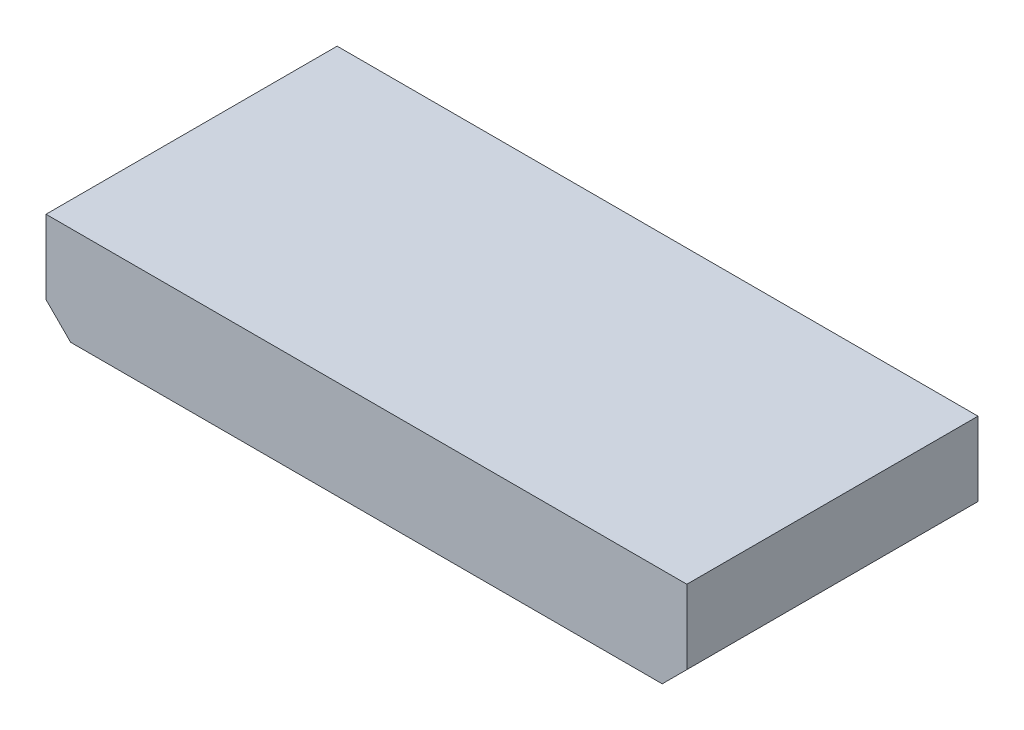
SolidWorks part; units mm, degrees
ref_plane "Front Plane" through (0, 0, 0) normal (0, 0, 1) x (1, 0, 0)
ref_plane "Top Plane" through (0, 0, 0) normal (0, 1, 0) x (1, 0, 0)
ref_plane "Right Plane" through (0, 0, 0) normal (1, 0, 0) x (0, 0, -1)
sketch "Sketch1" plane through (0, 0, 0) normal (0, 0, 1) x (1, 0, 0)
  line L0 (-5.08, 2.54) -> (-5.08, -1.27)
  line L1 (-5.08, -1.27) -> (-3.81, -2.54)
  line L2 (-3.81, -2.54) -> (26.67, -2.54)
  line L3 (26.67, -2.54) -> (27.94, -1.27)
  line L4 (27.94, -1.27) -> (27.94, 2.54)
  line L5 (27.94, 2.54) -> (-5.08, 2.54)
extrude "Component_Outline" add sketch "Sketch1" along normal blind 15 separate body
sketch "Sketch2" plane through (0, 0, 0) normal (0, 0, 1) x (1, 0, 0)
  circle A0 centre (0, 0) radius 0.25
extrude "1" add sketch "Sketch2" against normal blind 2 separate body
sketch "Sketch3" plane through (0, 0, 0) normal (0, 0, 1) x (1, 0, 0)
  circle A0 centre (2.54, 0) radius 0.25
extrude "2" add sketch "Sketch3" against normal blind 2 separate body
sketch "Sketch4" plane through (0, 0, 0) normal (0, 0, 1) x (1, 0, 0)
  circle A0 centre (5.08, 0) radius 0.25
extrude "3" add sketch "Sketch4" against normal blind 2 separate body
sketch "Sketch5" plane through (0, 0, 0) normal (0, 0, 1) x (1, 0, 0)
  circle A0 centre (7.62, 0) radius 0.25
extrude "4" add sketch "Sketch5" against normal blind 2 separate body
sketch "Sketch6" plane through (0, 0, 0) normal (0, 0, 1) x (1, 0, 0)
  circle A0 centre (10.16, 0) radius 0.25
extrude "5" add sketch "Sketch6" against normal blind 2 separate body
sketch "Sketch7" plane through (0, 0, 0) normal (0, 0, 1) x (1, 0, 0)
  circle A0 centre (12.7, 0) radius 0.25
extrude "6" add sketch "Sketch7" against normal blind 2 separate body
sketch "Sketch8" plane through (0, 0, 0) normal (0, 0, 1) x (1, 0, 0)
  circle A0 centre (15.24, 0) radius 0.25
extrude "7" add sketch "Sketch8" against normal blind 2 separate body
sketch "Sketch9" plane through (0, 0, 0) normal (0, 0, 1) x (1, 0, 0)
  circle A0 centre (17.78, 0) radius 0.25
extrude "8" add sketch "Sketch9" against normal blind 2 separate body
sketch "Sketch10" plane through (0, 0, 0) normal (0, 0, 1) x (1, 0, 0)
  circle A0 centre (20.32, 0) radius 0.25
extrude "9" add sketch "Sketch10" against normal blind 2 separate body
sketch "Sketch11" plane through (0, 0, 0) normal (0, 0, 1) x (1, 0, 0)
  circle A0 centre (22.86, 0) radius 0.25
extrude "10" add sketch "Sketch11" against normal blind 2 separate body
sketch3d "3DSketch1"
  line L0 (0, 0, 0) -> (1, 0, 0)
  line L1 (0, 0, 0) -> (0, 1, 0)
  line L2 (0, 0, 0) -> (0, 0, 1)
  point P0 (0, 0, 0)
